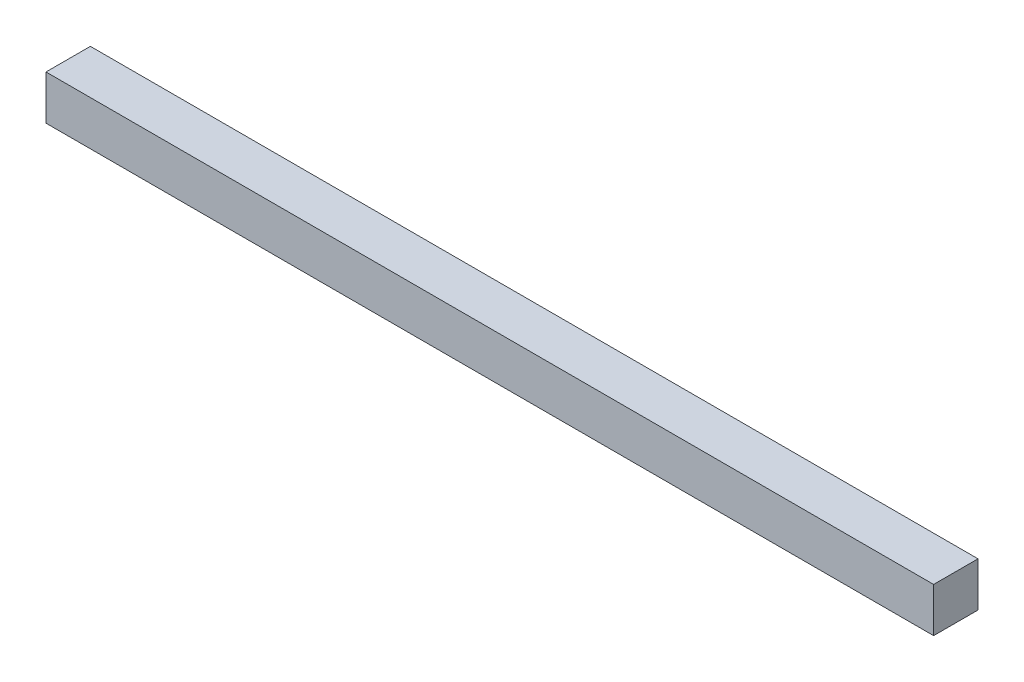
SolidWorks part; units mm, degrees
ref_plane "Front Plane" through (0, 0, 0) normal (0, 0, 1) x (1, 0, 0)
ref_plane "Top Plane" through (0, 0, 0) normal (0, 1, 0) x (1, 0, 0)
ref_plane "Right Plane" through (0, 0, 0) normal (1, 0, 0) x (0, 0, -1)
sketch "Sketch1" plane through (0, 0, 0) normal (0, 1, 0) x (1, 0, 0)
  line L1 (0, 0) -> (200, 0)
  line L2 (0, 0) -> (0, 10)
  line L3 (0, 10) -> (200, 10)
  line L4 (200, 0) -> (200, 10)
  dimension "D1" = 200
  dimension "w" = 10
extrude "Boss-Extrude1" add sketch "Sketch1" along normal blind 10
